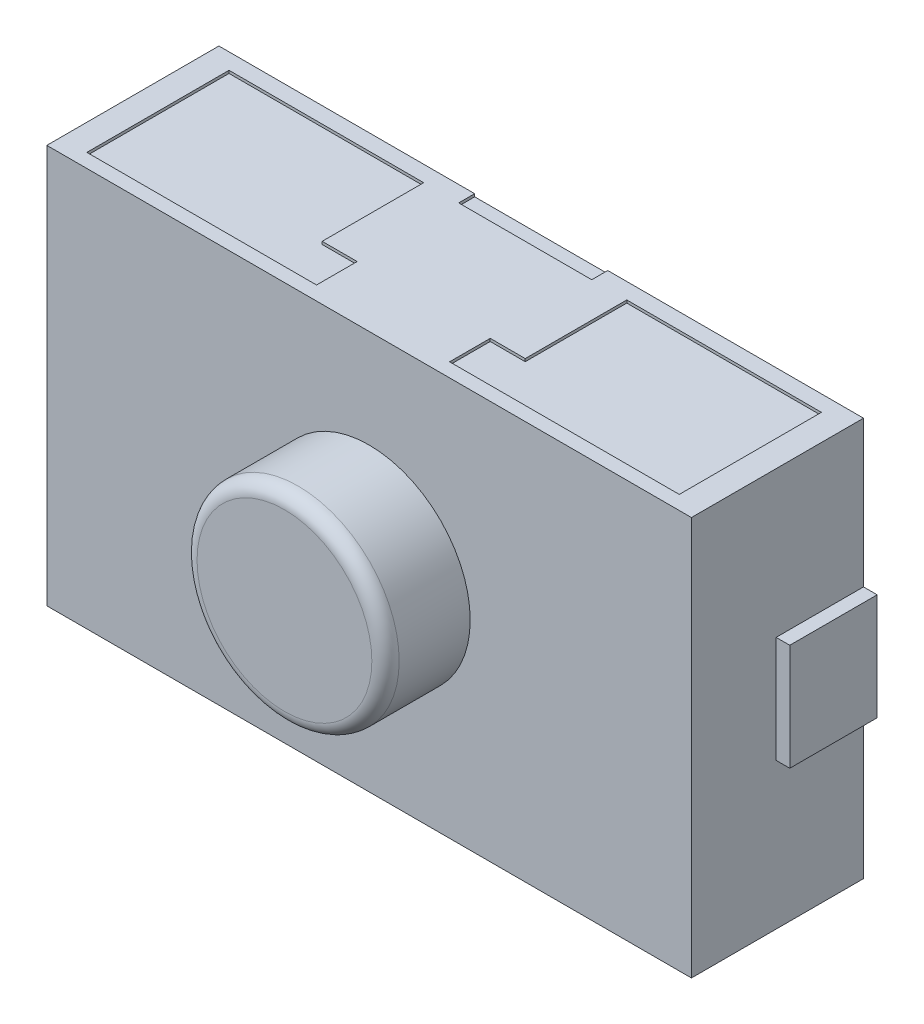
SolidWorks part; units mm, degrees
ref_plane "Front Plane" through (0, 0, 0) normal (0, 0, 1) x (1, 0, 0)
ref_plane "Top Plane" through (0, 0, 0) normal (0, 1, 0) x (1, 0, 0)
ref_plane "Right Plane" through (0, 0, 0) normal (1, 0, 0) x (0, 0, -1)
sketch "Sketch1" plane through (0, 0, 0) normal (0, 0, 1) x (1, 0, 0)
  line L1 (0, 0) -> (5.9944, 0)
  line L2 (0, 0) -> (0, 3.7084)
  line L3 (0, 3.7084) -> (5.9944, 3.7084)
  line L4 (5.9944, 0) -> (5.9944, 3.7084)
  dimension "D1" = 5.9944
  dimension "D2" = 3.7084
extrude "Boss-Extrude1" add sketch "Sketch1" along normal blind 1.6002
sketch "Sketch2" plane through (0, 0, 1.6002) normal (0, 0, 1) x (1, 0, 0)
  line L0 (0, 3.7084) -> (5.9944, 0) construction
  line L1 (2.9972, 1.8542) -> (5.9944, 3.7084) construction
  circle A0 centre (2.9972, 1.8542) radius 0.9398
  dimension "D1" = 1.8796
extrude "Boss-Extrude2" add sketch "Sketch2" along normal blind 0.7874
sketch "Sketch3" plane through (0, 0, 0) normal (-1, 0, 0) x (0, 0, 1)
  line L0 (0, 1.8542) -> (1.6002, 1.8542) construction
  line L1 (0, 3.7084) -> (0, 0) construction
  line L2 (1.6002, 3.7084) -> (1.6002, 0) construction
  line L4 (0, 2.3495) -> (0.8128, 2.3495)
  line L5 (0, 2.3495) -> (0, 1.3589)
  line L6 (0, 1.3589) -> (0.8128, 1.3589)
  line L7 (0.8128, 2.3495) -> (0.8128, 1.3589)
  dimension "D1" = 0.8128
  dimension "D2" = 0.9906
extrude "Boss-Extrude3" add sketch "Sketch3" along normal blind 0.127
sketch "Sketch4" plane through (5.9944, 0, 0) normal (1, 0, 0) x (0, 0, -1)
  line L1 (0, 2.3495) -> (-0.8128, 2.3495)
  line L2 (0, 2.3495) -> (0, 1.3589)
  line L3 (0, 1.3589) -> (-0.8128, 1.3589)
  line L4 (-0.8128, 2.3495) -> (-0.8128, 1.3589)
extrude "Boss-Extrude4" add sketch "Sketch4" along normal blind 0.127
sketch "Sketch5" plane through (0, 0, 0) normal (0, -1, 0) x (1, 0, 0)
  line L0 (2.9972, 1.6002) -> (2.9972, 0) construction
  line L1 (0, 1.6002) -> (5.9944, 1.6002) construction
  line L2 (0, 0) -> (5.9944, 0) construction
  line L3 (2.9972, 0) -> (0, 1.6002) construction
  line L4 (2.9972, 0) -> (5.9944, 1.6002) construction
  line L5 (2.9972, 0) -> (5.9944, 1.6002) construction
  line L6 (0.2427, 1.4706) -> (2.053, 1.4706)
  line L7 (0.2427, 1.4706) -> (0.2427, 0.1486)
  line L8 (0.2427, 0.1486) -> (2.053, 0.1486)
  line L9 (2.053, 1.4706) -> (2.053, 0.1486)
  line L10 (2.053, 1.4706) -> (2.3786, 1.4706)
  line L11 (2.053, 1.4706) -> (2.053, 1.0928)
  line L12 (2.053, 1.0928) -> (2.3786, 1.0928)
  line L13 (2.3786, 1.4706) -> (2.3786, 1.0928)
  line L14 (3.6158, 0) -> (2.3786, 0)
  line L15 (2.9972, 0) -> (2.9972, 0.1486)
  line L16 (3.6158, 0.1486) -> (2.3786, 0.1486)
  line L17 (2.3786, 0) -> (2.3786, 0.1486)
  line L18 (3.6158, 0) -> (3.6158, 0.1486)
  line L19 (3.6158, 1.4706) -> (3.6158, 1.0928)
  line L20 (3.9414, 1.0928) -> (3.6158, 1.0928)
  line L21 (3.9414, 1.4706) -> (3.9414, 1.0928)
  line L22 (3.9414, 1.4706) -> (3.6158, 1.4706)
  line L23 (3.9414, 1.4706) -> (3.9414, 0.1486)
  line L24 (5.7517, 0.1486) -> (3.9414, 0.1486)
  line L25 (5.7517, 1.4706) -> (5.7517, 0.1486)
  line L26 (5.7517, 1.4706) -> (3.9414, 1.4706)
  line M1 (0, 0) -> (5.9944, 0)
extrude "Cut-Extrude1" cut sketch "Sketch5" against normal blind 0.0254 contours L9 L6 L7 L8 | L13 L10 L9 L12 | L21 L22 L19 L20 | L25 L26 L21 L23 L24 | L17 L15 L16 M1 | L14 L18 L16 L15
sketch "Sketch6" plane through (0, 3.7084, 0) normal (0, 1, 0) x (1, 0, 0)
  line L36 (0.2427, -1.4706) -> (2.3786, -1.4706)
  line L37 (2.3786, -1.4706) -> (2.3786, -1.0928)
  line L38 (2.3786, -1.0928) -> (2.053, -1.0928)
  line L39 (2.053, -1.0928) -> (2.053, -0.1486)
  line L40 (2.053, -0.1486) -> (0.2427, -0.1486)
  line L41 (0.2427, -0.1486) -> (0.2427, -1.4706)
  line L42 (0.2427, -1.4706) -> (0.2297, -1.477)
  line L43 (3.6158, -1.4706) -> (5.7517, -1.4706)
  line L44 (5.7517, -1.4706) -> (5.7517, -0.1486)
  line L45 (5.7517, -0.1486) -> (3.9414, -0.1486)
  line L46 (3.9414, -0.1486) -> (3.9414, -1.0928)
  line L47 (3.9414, -1.0928) -> (3.6158, -1.0928)
  line L48 (3.6158, -1.0928) -> (3.6158, -1.4706)
  line L50 (2.3786, -0.1486) -> (3.6158, -0.1486)
  line L51 (2.3786, -0.1486) -> (2.3786, 0)
  line L52 (2.3786, 0) -> (3.6158, 0)
  line L53 (3.6158, -0.1486) -> (3.6158, 0)
extrude "Cut-Extrude2" cut sketch "Sketch6" against normal blind 0.0254 contours L47 L48 L43 L44 L45 L46 | L40 L41 L36 L37 L38 L39 | L52 L53 L50 L51
fillet "Fillet1" radius 0.127 1 edges at (3.937, 1.8542, 2.3876)
